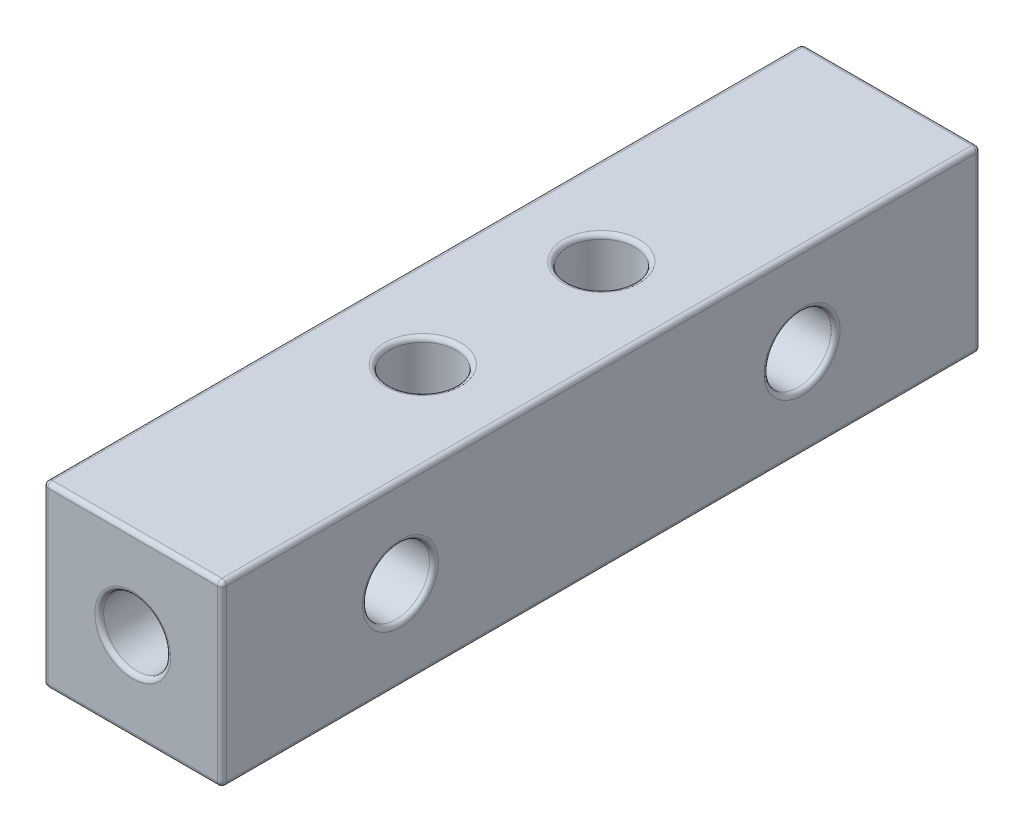
SolidWorks part; units mm, degrees
ref_plane "前视基准面" through (0, 0, 0) normal (0, 0, 1) x (1, 0, 0)
ref_plane "上视基准面" through (0, 0, 0) normal (0, 1, 0) x (1, 0, 0)
ref_plane "右视基准面" through (0, 0, 0) normal (1, 0, 0) x (0, 0, -1)
sketch "草图1" plane through (0, 0, 0) normal (0, 0, 1) x (1, 0, 0)
  line L1 (-4, 4) -> (4, 4)
  line L2 (-4, 4) -> (-4, -4)
  line L3 (-4, -4) -> (4, -4)
  line L4 (4, 4) -> (4, -4)
  line L5 (-4, 4) -> (4, -4) construction
  line L6 (-4, -4) -> (4, 4) construction
  point P0 (0, 0)
  dimension "D1" = 8
  dimension "D2" = 8
extrude "凸台-拉伸1" add sketch "草图1" along normal blind 34
sketch "草图2" plane through (0, 0, 34) normal (0, 0, 1) x (1, 0, 0)
  circle A0 centre (0, 0) radius 1.5
  dimension "D1" = 3
extrude "切除-拉伸1" cut sketch "草图2" against normal blind 10
sketch "草图3" plane through (0, 4, 0) normal (0, 1, 0) x (1, 0, 0)
  line L0 (0, 0) -> (0, -34) construction
  line L1 (4, -34) -> (-4, -34) construction
  line L2 (-4, -17) -> (4, -17) construction
  line L3 (-4, -34) -> (-4, 0) construction
  line L4 (4, -34) -> (4, 0) construction
  circle A0 centre (0, -21) radius 1.5
  circle A1 centre (0, -13) radius 1.5
  dimension "D1" = 3
  dimension "D2" = 8
extrude "切除-拉伸2" cut sketch "草图3" against normal through all
sketch "草图4" plane through (4, 0, 0) normal (1, 0, 0) x (0, 0, -1)
  line L0 (0, 0) -> (-34, 0) construction
  line L1 (0, -4) -> (0, 4) construction
  line L2 (-34, -4) -> (-34, 4) construction
  line L3 (-17, -4) -> (-17, 4) construction
  line L4 (-34, -4) -> (0, -4) construction
  line L5 (-34, 4) -> (0, 4) construction
  circle A0 centre (-8, 0) radius 1.5
  circle A1 centre (-26, 0) radius 1.5
  dimension "D1" = 3
  dimension "D2" = 18
extrude "切除-拉伸3" cut sketch "草图4" against normal through all
fillet "圆角1" radius 0.2 16 edges at (0, 4, 34) (4, 0, 34) (4, 4, 17) (0, 4, 0) (4, 0, 0) (0, -4, 34) (4, -4, 17) (0, -4, 0) (0, -4, 14.5) (0, -4, 22.5) (-4, 4, 17) (-4, 0, 34) (-4, -4, 17) (-4, 0, 0) (-4, -1.5, 26) (-4, 1.5, 8)
fillet "圆角2" radius 0.2 5 edges at (1.5, 0, 34) (4, 1.5, 8) (4, -1.5, 26) (0, 4, 22.5) (0, 4, 14.5)
